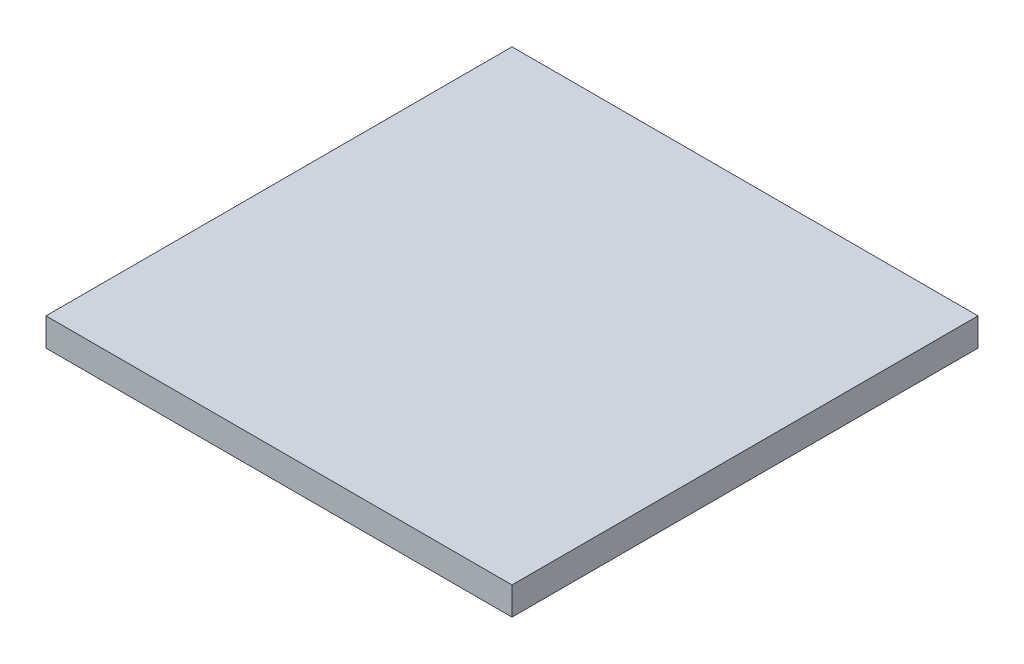
SolidWorks part; units mm, degrees
ref_plane "前视基准面" through (0, 0, 0) normal (0, 0, 1) x (1, 0, 0)
ref_plane "上视基准面" through (0, 0, 0) normal (0, 1, 0) x (1, 0, 0)
ref_plane "右视基准面" through (0, 0, 0) normal (1, 0, 0) x (0, 0, -1)
sketch "草图1" plane through (0, 0, 0) normal (0, 1, 0) x (1, 0, 0)
  line L1 (-25, 25) -> (25, 25)
  line L2 (-25, 25) -> (-25, -25)
  line L3 (-25, -25) -> (25, -25)
  line L4 (25, 25) -> (25, -25)
  line L5 (-25, 25) -> (25, -25) construction
  line L6 (-25, -25) -> (25, 25) construction
  point P0 (0, 0)
  dimension "D1" = 50
  dimension "D2" = 50
extrude "凸台-拉伸1" add sketch "草图1" along normal blind 3
